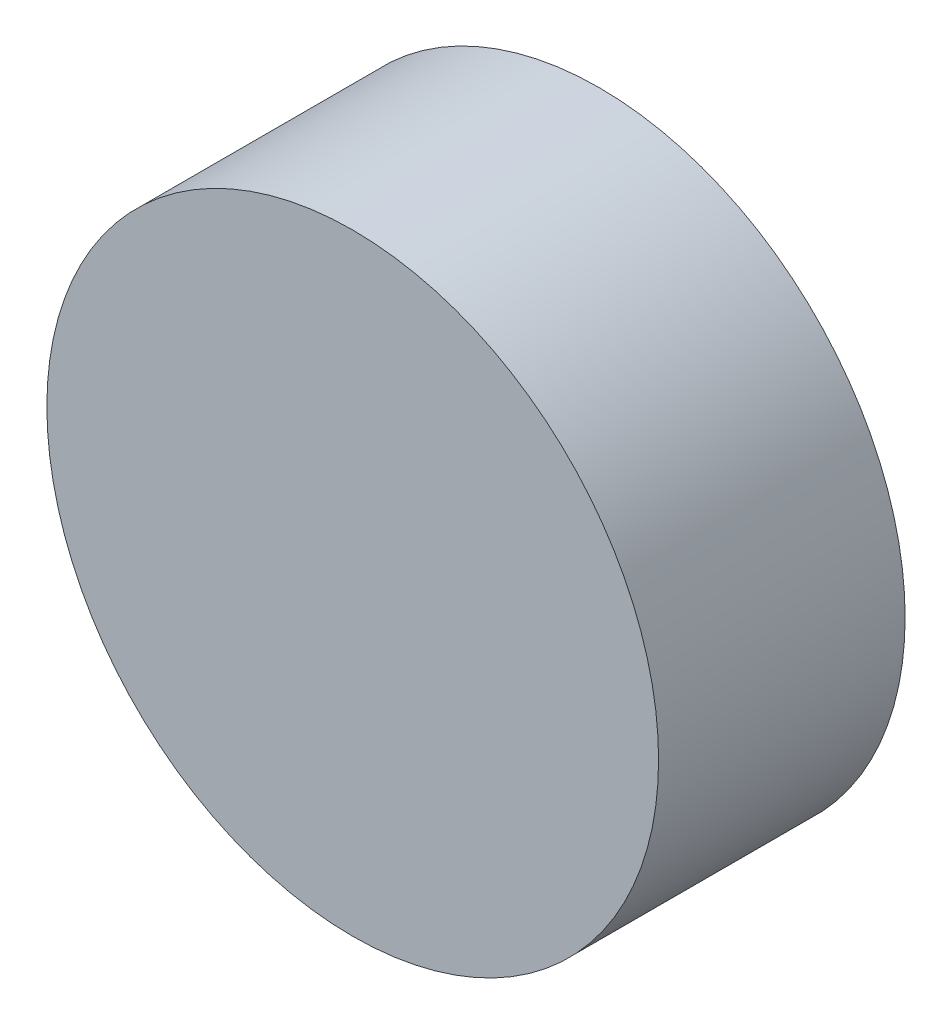
SolidWorks part; units mm, degrees
ref_plane "Front" through (0, 0, 0) normal (0, 0, 1) x (1, 0, 0)
ref_plane "Top" through (0, 0, 0) normal (0, 1, 0) x (1, 0, 0)
ref_plane "Right" through (0, 0, 0) normal (1, 0, 0) x (0, 0, -1)
sketch "Sketch1" plane through (0, 0, 0) normal (0, 0, 1) x (1, 0, 0)
  circle A0 centre (291.0984, 204.55) radius 12.7
  point P0 (291.0984, 204.55)
  dimension "D1" = 25.4
extrude "Boss-Extrude1" add sketch "Sketch1" along normal up to surface (10.2372 mm away) contours A0
